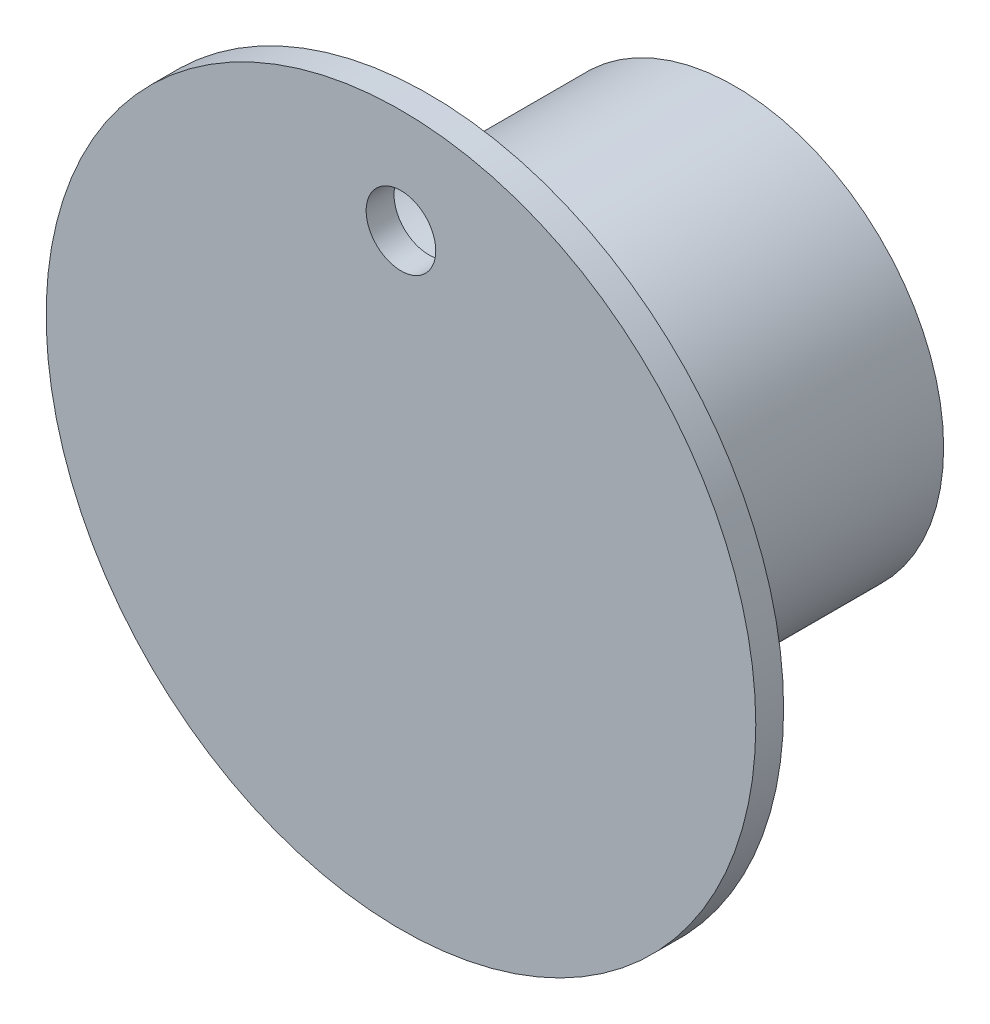
SolidWorks part; units mm, degrees
ref_plane "Plan de face" through (0, 0, 0) normal (0, 0, 1) x (1, 0, 0)
ref_plane "Plan de dessus" through (0, 0, 0) normal (0, 1, 0) x (1, 0, 0)
ref_plane "Plan de droite" through (0, 0, 0) normal (1, 0, 0) x (0, 0, -1)
sketch "Esquisse1" plane through (0, 0, 0) normal (0, 0, 1) x (1, 0, 0)
  circle A0 centre (0, 0) radius 25.5
  dimension "D2" = 51
extrude "Boss.-Extru.1" add sketch "Esquisse1" along normal blind 2
sketch "Esquisse2" plane through (0, 0, 0) normal (0, 0, -1) x (-1, 0, 0)
  circle A0 centre (0, 0) radius 10
  circle A1 centre (0, 0) radius 15
  dimension "D1" = 20
  dimension "D2" = 30
extrude "Boss.-Extru.2" add sketch "Esquisse2" along normal blind 22
sketch "Esquisse3" plane through (0, 0, 2) normal (0, 0, 1) x (1, 0, 0)
  line L0 (0, 0) -> (0, 18) construction
  circle A0 centre (0, 18) radius 2.5
  dimension "D2" = 5
  dimension "D1" = 18
extrude "Enlèv. mat.-Extru.1" cut sketch "Esquisse3" against normal blind 2
